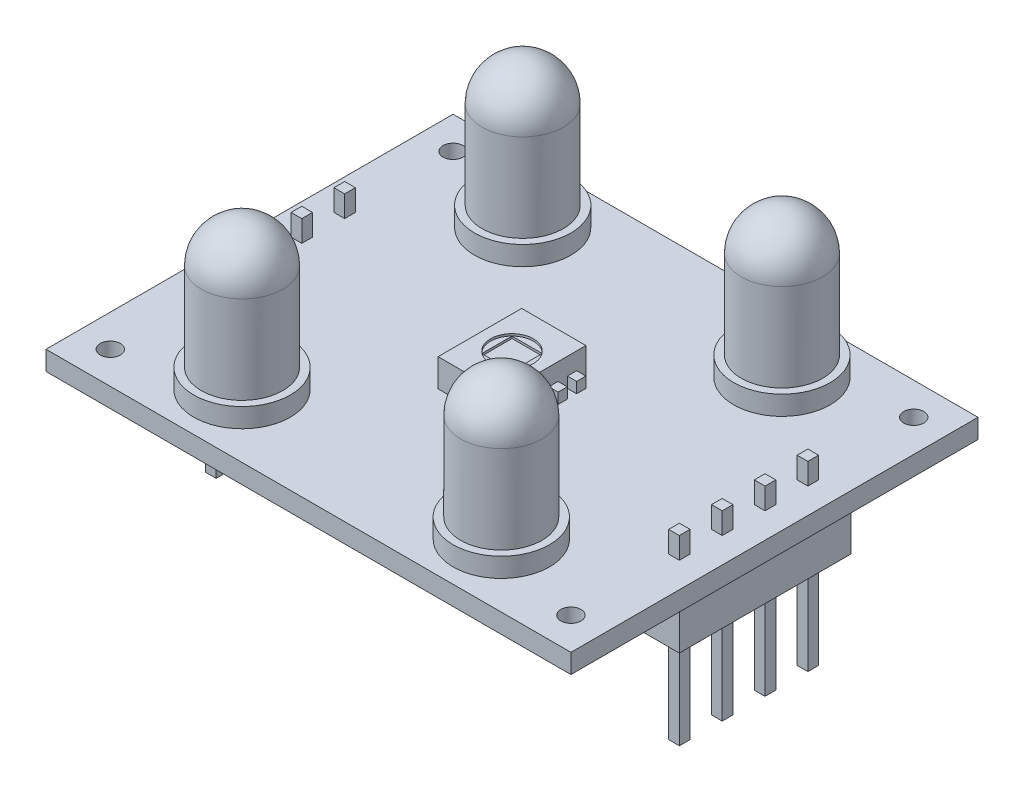
SolidWorks part; units mm, degrees
ref_plane "Plan de face" through (0, 0, 0) normal (0, 0, 1) x (1, 0, 0)
ref_plane "Plan de dessus" through (0, 0, 0) normal (0, 1, 0) x (1, 0, 0)
ref_plane "Plan de droite" through (0, 0, 0) normal (1, 0, 0) x (0, 0, -1)
sketch "Esquisse1" plane through (0, 0, 0) normal (0, 1, 0) x (1, 0, 0)
  line L1 (-15.5575, -12.065) -> (15.5575, -12.065)
  line L2 (-15.5575, -12.065) -> (-15.5575, 12.065)
  line L3 (-15.5575, 12.065) -> (15.5575, 12.065)
  line L4 (15.5575, -12.065) -> (15.5575, 12.065)
  line L5 (-15.5575, -12.065) -> (15.5575, 12.065) construction
  line L6 (-15.5575, 12.065) -> (15.5575, -12.065) construction
  line L7 (13.6525, -10.16) -> (-13.6525, -10.16) construction
  line L8 (13.6525, -10.16) -> (13.6525, 10.16) construction
  line L9 (13.6525, 10.16) -> (-13.6525, 10.16) construction
  line L10 (-13.6525, -10.16) -> (-13.6525, 10.16) construction
  line L11 (13.6525, -10.16) -> (-13.6525, 10.16) construction
  line L12 (13.6525, 10.16) -> (-13.6525, -10.16) construction
  circle A0 centre (-13.6525, 10.16) radius 0.5953
  circle A1 centre (13.6525, 10.16) radius 0.5953
  circle A2 centre (-13.6525, -10.16) radius 0.5953
  circle A3 centre (13.6525, -10.16) radius 0.5953
  point P0 (0, 0)
  point P6 (0, 0)
  point P8 (0, 0)
  point P10 (0, 0)
  point P18 (0, 0)
  dimension "D5" = 1.1906
  dimension "D1" = 31.115
  dimension "D2" = 24.13
  dimension "D3" = 1.905
  dimension "D4" = 1.905
extrude "Boss.-Extru.1" add sketch "Esquisse1" along normal mid plane 1.143
sketch "Esquisse2" plane through (0, 0, 0) normal (0, 0, 1) x (1, 0, 0)
  line L0 (-15.5575, 0.5715) -> (15.5575, 0.5715) construction
  line L1 (-1.905, 2.2225) -> (1.905, 2.2225)
  line L2 (-1.905, 2.2225) -> (-1.905, 0.5715)
  line L3 (-1.905, 0.5715) -> (1.905, 0.5715)
  line L4 (1.905, 2.2225) -> (1.905, 0.5715)
  line L5 (-1.905, 2.2225) -> (1.905, 0.5715) construction
  line L6 (-1.905, 0.5715) -> (1.905, 2.2225) construction
  point P0 (0, 1.397)
  point P7 (0, 0)
  dimension "D1" = 1.651
  dimension "D2" = 3.81
extrude "Boss.-Extru.2" add sketch "Esquisse2" along normal mid plane 4.953
sketch "Esquisse3" plane through (0, 0.5715, 0) normal (0, 1, 0) x (1, 0, 0)
  line L0 (1.905, -2.4765) -> (1.905, 2.4765) construction
  line L1 (1.905, 1.9262) -> (2.4553, 1.9262)
  line L2 (1.905, 1.9262) -> (1.905, 1.3758)
  line L3 (1.905, 1.3758) -> (2.4553, 1.3758)
  line L4 (2.4553, 1.9262) -> (2.4553, 1.3758)
  line L5 (2.1802, 1.3758) -> (2.1802, 0.8255) construction
  line L6 (1.905, 0.8255) -> (2.4553, 0.8255)
  line L7 (1.905, 0.8255) -> (1.905, 0.2752)
  line L8 (1.905, 0.2752) -> (2.4553, 0.2752)
  line L9 (2.4553, 0.8255) -> (2.4553, 0.2752)
  line L10 (1.905, -0.2752) -> (2.4553, -0.2752)
  line L11 (1.905, -0.2752) -> (1.905, -0.8255)
  line L12 (1.905, -0.8255) -> (2.4553, -0.8255)
  line L13 (2.4553, -0.2752) -> (2.4553, -0.8255)
  line L14 (1.905, -1.3758) -> (2.4553, -1.3758)
  line L15 (1.905, -1.3758) -> (1.905, -1.9262)
  line L16 (1.905, -1.9262) -> (2.4553, -1.9262)
  line L17 (2.4553, -1.3758) -> (2.4553, -1.9262)
  line L18 (2.1802, 0.2752) -> (2.1802, -0.2752) construction
  line L19 (2.1802, -0.8255) -> (2.1802, -1.3758) construction
  line L20 (2.1802, 1.9262) -> (2.1802, 2.4765) construction
  line L21 (2.1802, -1.9262) -> (2.1802, -2.4765) construction
  line L22 (-1.905, -2.4765) -> (1.905, -2.4765) construction
  line L23 (1.905, 2.4765) -> (-1.905, 2.4765) construction
  point P28 (0, 0)
  point P31 (0, 0)
extrude "Boss.-Extru.3" add sketch "Esquisse3" along normal blind 0.635
sketch "Esquisse9" plane through (0, -0.5715, 0) normal (0, -1, 0) x (1, 0, 0)
  line L0 (0, -5.2776) -> (0, 5.2776) construction
  line L1 (15, 5.08) -> (12.46, 5.08)
  line L2 (15, 5.08) -> (15, -5.08)
  line L3 (15, -5.08) -> (12.46, -5.08)
  line L4 (12.46, 5.08) -> (12.46, -5.08)
  line L5 (0, -1.5367) -> (0, 1.5367) construction
  point P6 (12.46, 0)
  dimension "D1" = 2.54
  dimension "D2" = 10.16
  dimension "D3" = 30
extrude "Boss.-Extru.6" add sketch "Esquisse9" along normal blind 2.667
sketch "Esquisse10" plane through (0, -3.2385, 0) normal (0, -1, 0) x (1, 0, 0)
  line L0 (12.46, 0) -> (15, 5.08) construction
  line L1 (12.46, 5.08) -> (12.46, -5.08) construction
  line L2 (13.73, 2.54) -> (13.73, 5.08) construction
  line L3 (15, 5.08) -> (12.46, 5.08) construction
  line L4 (12.46, 0) -> (15, -5.08) construction
  line L5 (13.73, -2.54) -> (13.73, -5.08) construction
  line L6 (12.46, -5.08) -> (15, -5.08) construction
  line L7 (13.73, 2.54) -> (13.73, 0) construction
  line L8 (13.4125, 4.1275) -> (14.0475, 4.1275)
  line L9 (13.4125, 4.1275) -> (13.4125, 3.4925)
  line L10 (13.4125, 3.4925) -> (14.0475, 3.4925)
  line L11 (14.0475, 4.1275) -> (14.0475, 3.4925)
  line L12 (13.4125, 4.1275) -> (14.0475, 3.4925) construction
  line L13 (13.4125, 3.4925) -> (14.0475, 4.1275) construction
  line L14 (3.0035, 0) -> (-3.0035, 0) construction
  line L15 (13.73, 0) -> (13.73, -2.54) construction
  line L17 (13.4125, 1.5875) -> (14.0475, 1.5875)
  line L18 (13.4125, 1.5875) -> (13.4125, 0.9525)
  line L19 (13.4125, 0.9525) -> (14.0475, 0.9525)
  line L20 (14.0475, 1.5875) -> (14.0475, 0.9525)
  line L21 (13.4125, 1.5875) -> (14.0475, 0.9525) construction
  line L22 (13.4125, 0.9525) -> (14.0475, 1.5875) construction
  line L23 (13.4125, -0.9525) -> (14.0475, -0.9525)
  line L24 (13.4125, -0.9525) -> (13.4125, -1.5875)
  line L25 (13.4125, -1.5875) -> (14.0475, -1.5875)
  line L26 (14.0475, -0.9525) -> (14.0475, -1.5875)
  line L27 (13.4125, -0.9525) -> (14.0475, -1.5875) construction
  line L28 (13.4125, -1.5875) -> (14.0475, -0.9525) construction
  line L29 (13.4125, -3.4925) -> (14.0475, -3.4925)
  line L30 (13.4125, -3.4925) -> (13.4125, -4.1275)
  line L31 (13.4125, -4.1275) -> (14.0475, -4.1275)
  line L32 (14.0475, -3.4925) -> (14.0475, -4.1275)
  line L33 (13.4125, -3.4925) -> (14.0475, -4.1275) construction
  line L34 (13.4125, -4.1275) -> (14.0475, -3.4925) construction
  point P13 (13.73, 3.81)
  point P18 (13.73, 1.27)
  point P28 (13.73, -1.27)
  point P33 (13.73, -3.81)
  dimension "D1" = 0.635
extrude "Boss.-Extru.7" add sketch "Esquisse10" along normal blind 5.715 and the other way offset from surface (5.08 mm away) 1.27 other way up to face at (0, 0.5715, 0)
mirror "Symétrie1" about plane through (0, 0, 0) normal (1, 0, 0) of "Boss.-Extru.7", "Boss.-Extru.3"
mirror "Symétrie2" about plane through (0, 0, 0) normal (1, 0, 0) of "Boss.-Extru.6"
sketch "Esquisse4" plane through (0, 2.2225, 0) normal (0, 1, 0) x (1, 0, 0)
  circle A0 centre (0, 0) radius 1.27
  dimension "D1" = 2.54
extrude "Enlèv. mat.-Extru.1" cut sketch "Esquisse4" against normal blind 0.127
sketch "Esquisse5" plane through (0, 2.0955, 0) normal (0, 1, 0) x (1, 0, 0)
  line L1 (0.898, -0.898) -> (-0.898, -0.898)
  line L2 (0.898, -0.898) -> (0.898, 0.898)
  line L3 (0.898, 0.898) -> (-0.898, 0.898)
  line L4 (-0.898, -0.898) -> (-0.898, 0.898)
  line L5 (0.898, -0.898) -> (-0.898, 0.898) construction
  line L6 (0.898, 0.898) -> (-0.898, -0.898) construction
  circle A0 centre (0, 0) radius 1.27 construction
  point P0 (0, 0)
extrude "Enlèv. mat.-Extru.2" cut sketch "Esquisse5" against normal blind 0.127
sketch "Esquisse6" plane through (0, 0.5715, 0) normal (0, 1, 0) x (1, 0, 0)
  line L1 (7.6835, -8.3185) -> (-7.6835, -8.3185) construction
  line L2 (7.6835, -8.3185) -> (7.6835, 8.3185) construction
  line L3 (7.6835, 8.3185) -> (-7.6835, 8.3185) construction
  line L4 (-7.6835, -8.3185) -> (-7.6835, 8.3185) construction
  line L5 (7.6835, -8.3185) -> (-7.6835, 8.3185) construction
  line L6 (7.6835, 8.3185) -> (-7.6835, -8.3185) construction
  point P6 (0, 0)
  point P7 (-7.6835, 8.3185)
  point P8 (7.6835, 8.3185)
  point P9 (7.6835, -8.3185)
  point P10 (-7.6835, -8.3185)
  point P11 (-7.5057, -11.3417)
  point P12 (0, 0)
  dimension "D1" = 15.367
  dimension "D2" = 16.637
sketch "Esquisse7" plane through (0, 0.5715, 0) normal (0, 1, 0) x (1, 0, 0)
  circle A0 centre (-7.6835, 8.3185) radius 2.8575
  dimension "D1" = 5.715
extrude "Boss.-Extru.4" add sketch "Esquisse7" along normal blind 1.143
sketch "Esquisse8" plane through (0, 1.7145, 0) normal (0, 1, 0) x (1, 0, 0)
  circle A0 centre (-7.6835, 8.3185) radius 2.413
  dimension "D1" = 4.826
extrude "Boss.-Extru.5" add sketch "Esquisse8" along normal blind 7.62
fillet "Congé1" radius 2.413 1 edges at (-7.6835, 9.3345, -5.9055)
pattern_sketch "Répét. par esquisse1" of "Boss.-Extru.4", "Boss.-Extru.5", "Congé1" driven by "Esquisse6"
